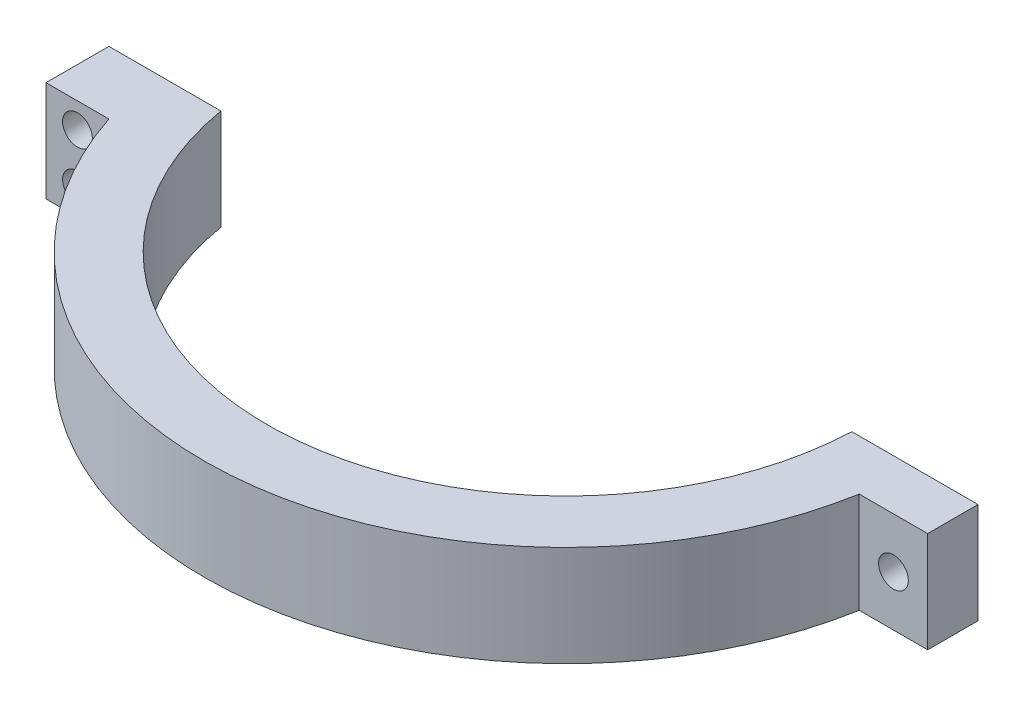
SolidWorks part; units mm, degrees
material "1060 Alloy"
ref_plane "Front Plane" through (0, 0, 0) normal (0, 0, 1) x (1, 0, 0)
ref_plane "Top Plane" through (0, 0, 0) normal (0, 1, 0) x (1, 0, 0)
ref_plane "Right Plane" through (0, 0, 0) normal (1, 0, 0) x (0, 0, -1)
sketch "Sketch1" plane through (0, 0, 0) normal (0, 1, 0) x (1, 0, 0)
  line L0 (0, 0) -> (-12.7, 0)
  line L1 (0, 0) -> (0, -6.35)
  line L2 (0, -6.35) -> (-6.9064, -6.35)
  line L3 (-72.5941, -5.08) -> (-83.8898, -5.08)
  line L4 (-83.8898, -5.08) -> (-83.8898, -11.43)
  line L5 (-83.8898, -11.43) -> (-77.5398, -11.43)
  arc A0 (-12.7, 0) -> (-72.5941, -5.08) centre (-42.8625, 0) cw
  arc A1 (-77.5398, -11.43) -> (-6.9064, -6.35) centre (-42.8625, 0) ccw
  dimension "D2" = 30.1625
  dimension "D3" = 6.35
  dimension "D1" = 5.08
  dimension "D4" = 12.7
  dimension "D5" = 6.35
  dimension "D6" = 6.35
  dimension "D7" = 6.35
extrude "Boss-Extrude1" add sketch "Sketch1" along normal blind 10.16
sketch "Sketch2" plane through (0, 0, 5.08) normal (0, 0, -1) x (-1, 0, 0)
  line L0 (80.7148, 2.54) -> (80.7148, 7.62) construction
  line L1 (83.8898, 10.16) -> (83.8898, 0) construction
  line L3 (83.8898, 10.16) -> (77.5398, 10.16) construction
  circle A0 centre (80.7148, 7.62) radius 1.5
  circle A1 centre (80.7148, 2.54) radius 1.5
  point P7 (80.7148, 5.08)
  point P9 (83.8898, 5.08)
  point P12 (80.7148, 10.16)
  dimension "D2" = 3
  dimension "D1" = 5.08
extrude "Cut-Extrude1" cut sketch "Sketch2" against normal through all
sketch "Sketch3" plane through (0, 0, 6.35) normal (0, 0, 1) x (1, 0, 0)
  line L0 (0, 0) -> (-6.9064, 10.16) construction
  circle A0 centre (-3.4532, 5.08) radius 1.5
  point P6 (-3.4532, 5.08)
  dimension "D1" = 3
extrude "Cut-Extrude2" cut sketch "Sketch3" against normal through all
sketch "Sketch4" plane through (0, 0, 0) normal (0, -1, 0) x (1, 0, 0)
  line L0 (0, 6.35) -> (0, 0) construction
  line L1 (-12.7267, 0) -> (0, 0)
  line L2 (-12.7267, 0) -> (-12.7267, 1.27)
  line L3 (-12.7267, 1.27) -> (0, 1.27)
  line L4 (0, 0) -> (0, 1.27)
  line L5 (0, 0) -> (-12.7, 0) construction
  arc A0 (-12.7, 0) -> (-72.5941, 5.08) centre (-42.8625, 0) ccw construction
  dimension "D1" = 1.27
extrude "Cut-Extrude3" cut sketch "Sketch4" against normal through all
